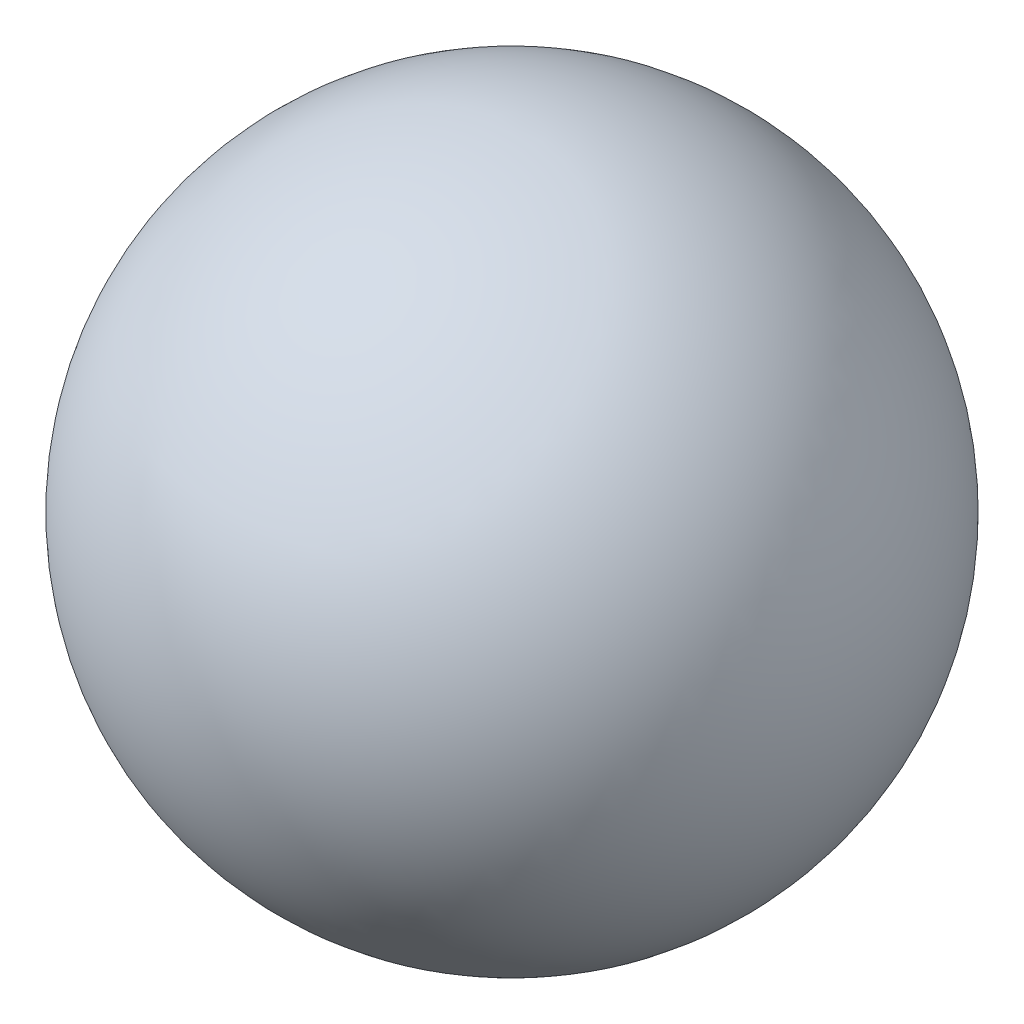
SolidWorks part; units mm, degrees
material "PE Low Density Film"
ref_plane "Front Plane" through (0, 0, 0) normal (0, 0, 1) x (1, 0, 0)
ref_plane "Top Plane" through (0, 0, 0) normal (0, 1, 0) x (1, 0, 0)
ref_plane "Right Plane" through (0, 0, 0) normal (1, 0, 0) x (0, 0, -1)
sketch "Sketch2" plane through (0, 0, 0) normal (0, 0, 1) x (1, 0, 0)
  line L0 (0, 0) -> (0, 600) construction
  arc A0 (0, 600) -> (0, 0) centre (0, 300) cw
  dimension "D1" = 600
revolve "Revolve-Thin1" add sketch "Sketch2" angle 360 about L0
